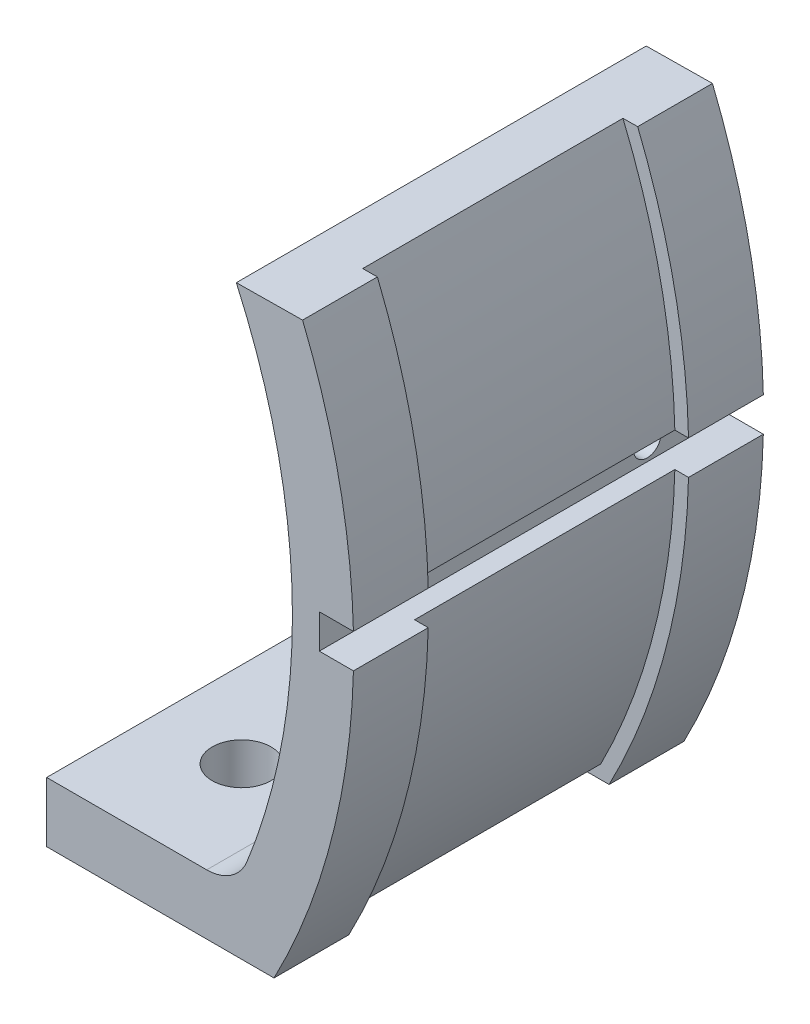
SolidWorks part; units mm, degrees
ref_plane "Front Plane" through (0, 0, 0) normal (0, 0, 1) x (1, 0, 0)
ref_plane "Top Plane" through (0, 0, 0) normal (0, 1, 0) x (1, 0, 0)
ref_plane "Right Plane" through (0, 0, 0) normal (1, 0, 0) x (0, 0, -1)
ref_plane "Plane1"
sketch "Sketch1" plane through (0, 0, 0) normal (0, 0, 1) x (1, 0, 0)
  line L0 (47.0635, 19.1234) -> (42.2139, 19.07)
  line L1 (42.1402, -19.2312) -> (27.0636, -19.2312)
  line L2 (27.0636, -19.2312) -> (27.0636, -22.1235)
  line L3 (27.0636, -22.1235) -> (27.0636, -23.6235)
  line L4 (27.0636, -23.6235) -> (44.973, -23.6235)
  line L5 (50.7848, -1.2499) -> (48.2849, -1.2501)
  line L6 (48.2849, -1.2501) -> (48.2849, 1.2499)
  line L7 (48.2849, 1.2499) -> (50.7849, 1.2499)
  arc A0 (42.1402, -19.2312) -> (42.2139, 19.07) centre (0, 0.0005) ccw
  arc A1 (44.973, -23.6235) -> (50.7848, -1.2499) centre (0, 0.0005) ccw
  arc A2 (50.7849, 1.2499) -> (47.0635, 19.1234) centre (0, 0.0005) ccw
  dimension "D1" = 2.5
  dimension "D2" = 2.5
  dimension "D3" = 1.5
extrude "Extrusion1" add sketch "Sketch1" along normal blind 30
fillet "Fillet1" radius 3.175 1 edges at (42.1402, -19.2312, 15)
sketch "Sketch2" plane through (48.2849, 0, 0) normal (1, 0, 0) x (0, 0, -1)
  circle A0 centre (-24, -0.0001) radius 1
  circle A1 centre (-6, -0.0001) radius 1
  dimension "D3" = 2
  dimension "D4" = 2
  dimension "D1" = 24.0325
  dimension "D2" = 18
extrude "Extrusion8" cut sketch "Sketch2" against normal blind 2
sketch "Sketch3" plane through (0, -19.2312, 0) normal (0, 1, 0) x (-1, 0, 0)
  circle A0 centre (-34.6019, 8) radius 2.15
  circle A1 centre (-34.6019, 22) radius 2.15
  dimension "D1" = 4.3
  dimension "D2" = 4.3
extrude "Extrusion11" cut sketch "Sketch3" against normal through all
ref_plane "Plane2"
sketch "Sketch4" plane through (0, 0, 15) normal (0, 0, 1) x (1, 0, 0)
  line L0 (47.0635, 19.1234) -> (45.987, 19.1116)
  line L1 (49.7843, 1.2499) -> (50.7849, 1.2499)
  line L2 (27.0636, -23.6235) -> (44.973, -23.6235)
  line L3 (50.7848, -1.2499) -> (49.7843, -1.2499)
  line L4 (44.3643, -22.6235) -> (27.0636, -22.6235)
  line L5 (27.0636, -22.6235) -> (27.0636, -23.6235)
  arc A0 (49.7843, 1.2499) -> (45.987, 19.1116) centre (0, 0.0005) ccw
  arc A1 (50.7849, 1.2499) -> (47.0635, 19.1234) centre (0, 0.0005) ccw
  arc A2 (44.973, -23.6235) -> (50.7848, -1.2499) centre (0, 0.0005) ccw
  arc A3 (44.3643, -22.6235) -> (49.7843, -1.2499) centre (0, 0.0005) ccw
  dimension "D1" = 1
extrude "Extrusion12" cut sketch "Sketch4" against normal mid plane 19.05 contours L1 A1 L0 A0 | A3 L4 L5 L2 A2 L3
sketch "Sketch5" plane through (27.0636, 0, 0) normal (-1, 0, 0) x (0, 0, 1)
  line L0 (0, -19.2312) -> (0, -23.6235)
  line L1 (0, -23.6235) -> (5.475, -23.6235)
  line L2 (5.475, -23.6235) -> (5.475, -22.6235)
  line L3 (5.475, -22.6235) -> (24.525, -22.6235)
  line L4 (24.525, -22.6235) -> (24.525, -23.6235)
  line L5 (24.525, -23.6235) -> (30, -23.6235)
  line L6 (30, -23.6235) -> (30, -19.2312)
  line L7 (30, -19.2312) -> (0, -19.2312)
extrude "Cut-Extrude1" cut sketch "Sketch5" against normal blind 1.27
